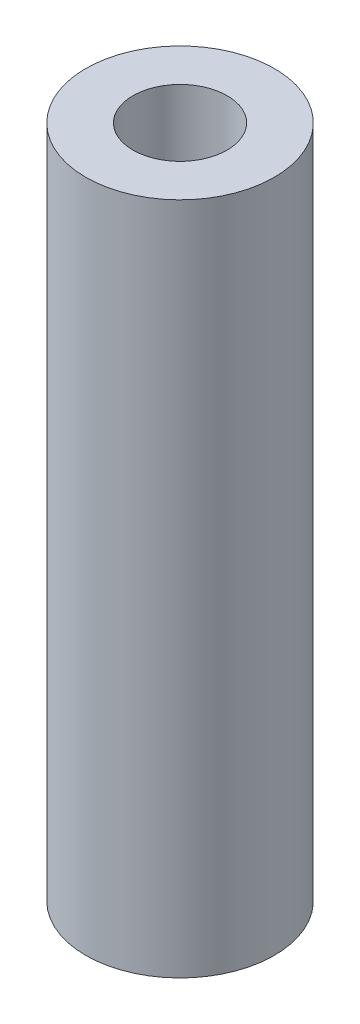
SolidWorks part; units mm, degrees
ref_plane "Front Plane" through (0, 0, 0) normal (0, 0, 1) x (1, 0, 0)
ref_plane "Top Plane" through (0, 0, 0) normal (0, 1, 0) x (1, 0, 0)
ref_plane "Right Plane" through (0, 0, 0) normal (1, 0, 0) x (0, 0, -1)
sketch "Sketch1" plane through (0, 0, 0) normal (0, 1, 0) x (1, 0, 0)
  circle A0 centre (0, 0) radius 4
  circle A1 centre (0, 0) radius 2
  dimension "D1" = 4
  dimension "D2" = 2
extrude "Boss-Extrude1" add sketch "Sketch1" along normal blind 28.6
